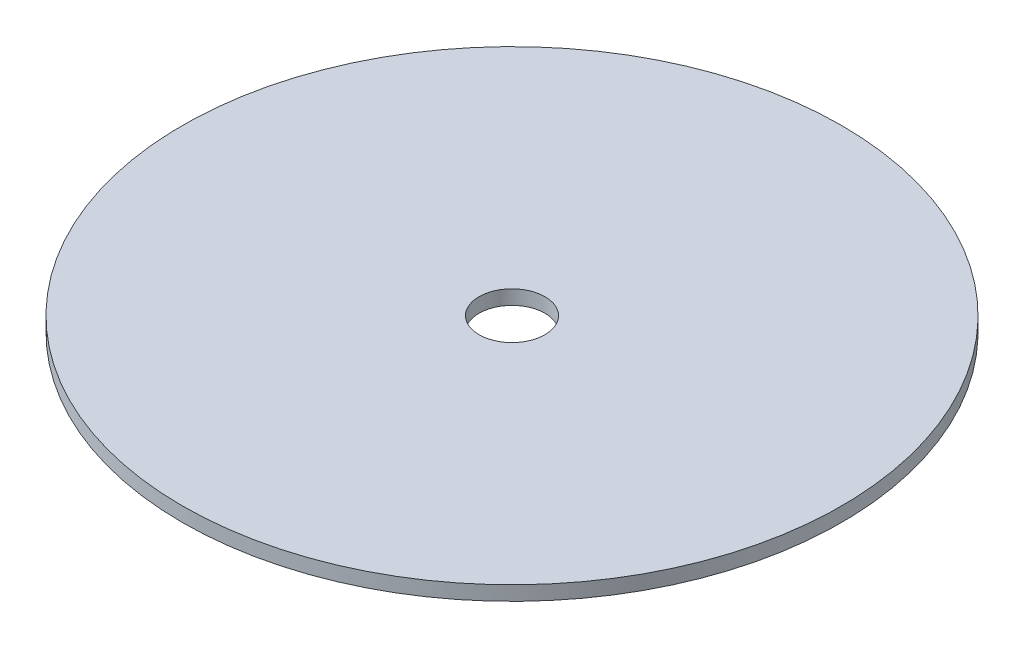
SolidWorks part; units mm, degrees
material "Corrugated Cardboard"
ref_plane "Front Plane" through (0, 0, 0) normal (0, 0, 1) x (1, 0, 0)
ref_plane "Top Plane" through (0, 0, 0) normal (0, 1, 0) x (1, 0, 0)
ref_plane "Right Plane" through (0, 0, 0) normal (1, 0, 0) x (0, 0, -1)
sketch "Sketch1" plane through (0, 0, 0) normal (0, 1, 0) x (1, 0, 0)
  circle A0 centre (0, 0) radius 114.3
  circle A1 centre (0, 0) radius 9.525
  dimension "D1" = 228.6
  dimension "D2" = 19.05
extrude "Boss-Extrude1" add sketch "Sketch1" along normal blind 4.16
sketch "Sketch2" plane through (0, 4.16, 0) normal (0, 1, 0) x (1, 0, 0)
  circle A0 centre (0, 0) radius 95.25
  circle A1 centre (0, 0) radius 131.9506
  dimension "D1" = 190.5
extrude "Cut-Extrude1" cut sketch "Sketch2" against normal through all
sketch "Sketch3" [suppressed] plane through (0, 4.16, 0) normal (0, 1, 0) x (1, 0, 0)
  circle A0 centre (0, 0) radius 63.5
  circle A1 centre (0, 0) radius 112.5748
  dimension "D1" = 127
extrude "Cut-Extrude2" [suppressed] cut sketch "Sketch3" against normal through all
